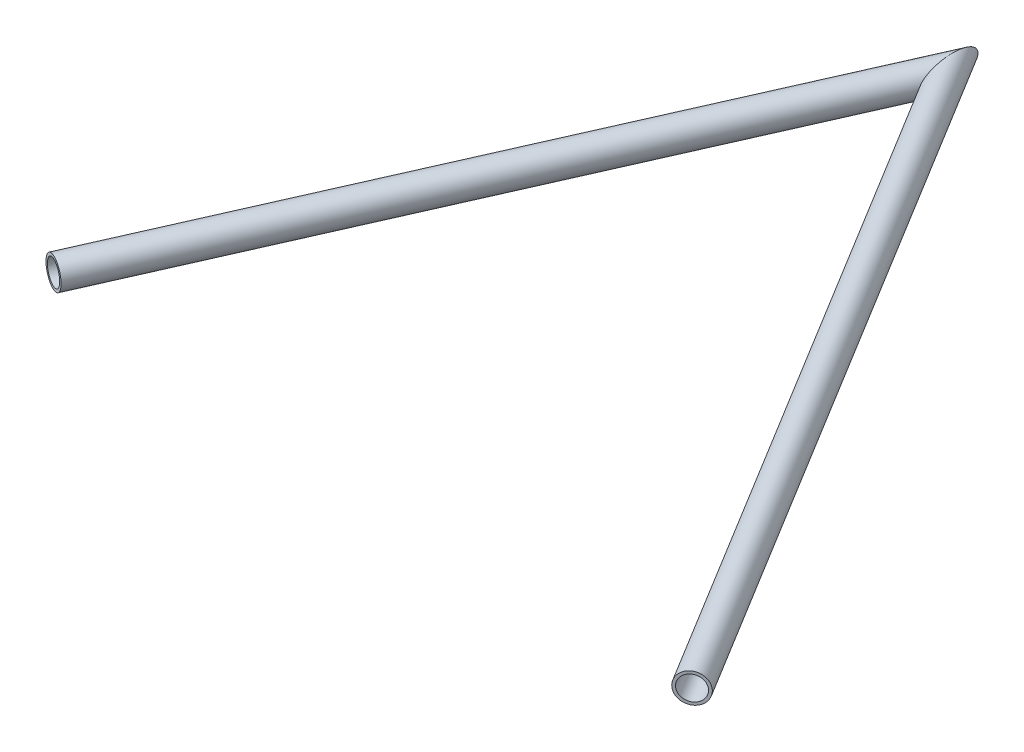
SolidWorks part; units mm, degrees
ref_plane "Front" through (0, 0, 0) normal (0, 0, 1) x (1, 0, 0)
ref_plane "Top" through (0, 0, 0) normal (0, 1, 0) x (1, 0, 0)
ref_plane "Right" through (0, 0, 0) normal (1, 0, 0) x (0, 0, -1)
sketch "Sketch3" plane through (0, 0, 0) normal (0, 1, 0) x (1, 0, 0)
  line L0 (0, 0) -> (-147.4476, -333.4965)
  line L1 (0, 0) -> (217.5524, -355.3339)
  line L2 (-147.4476, -333.4965) -> (217.5524, -355.3339) construction
  line L3 (0, 0) -> (0, -342.3181) construction
  circle A0 centre (-147.4476, -333.4965) radius 14.6812 construction
  circle A1 centre (217.5524, -355.3339) radius 14.6812 construction
  dimension "D1" = 29.3624
  dimension "D2" = 364.6377
  dimension "D3" = 416.6429
  dimension "D5" = 147.7112
  dimension "D6" = 365.6527
other "Structural Member1"
ref_plane "Plane1" through (0, 0, 0) normal (-0.4044, 0, 0.9146) x (0.9146, 0, 0.4044)
sketch "Sketch1" plane through (0, 0, 0) normal (-0.4044, 0, 0.9146) x (0.9146, 0, 0.4044)
  circle A0 centre (0, 0) radius 6.4643
  circle A1 centre (0, 0) radius 7.9375
  point P5 (0, 0)
  dimension "Out_dia" = 15.875
  dimension "D1" = 1.4732
